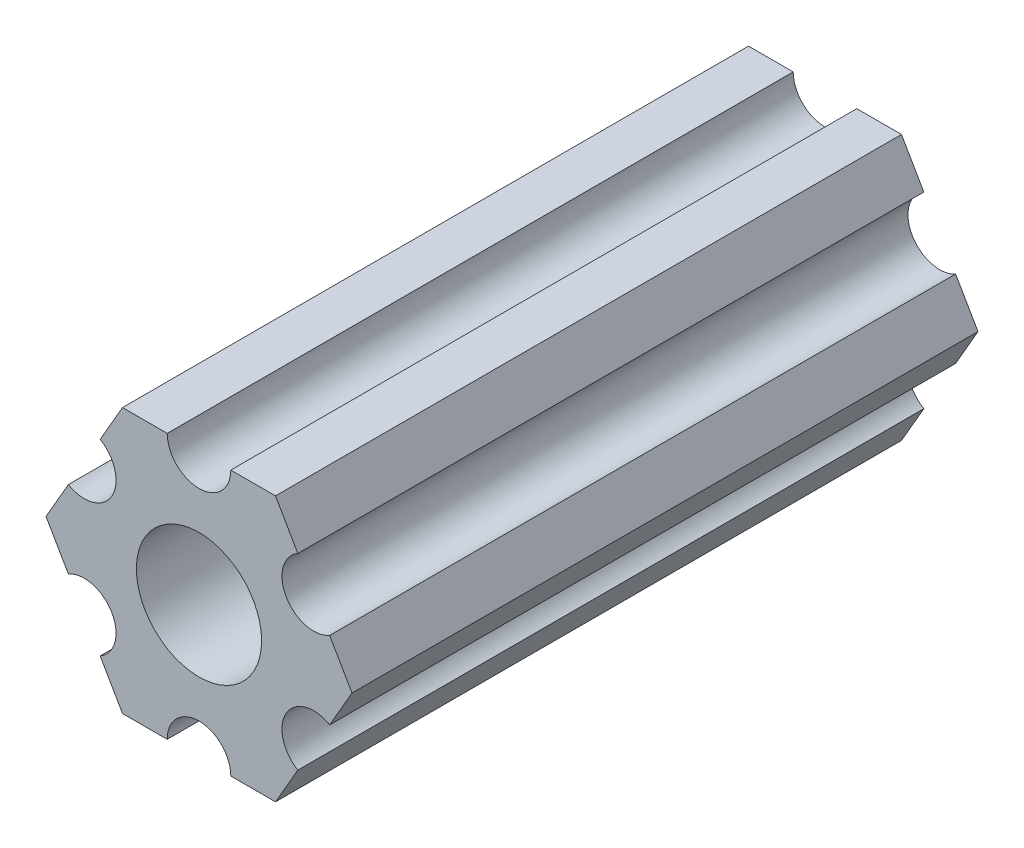
SolidWorks part; units mm, degrees
material "Churro - 6005A-T61"
ref_plane "Plano frontal" through (0, 0, 0) normal (0, 0, 1) x (1, 0, 0)
ref_plane "Plano superior" through (0, 0, 0) normal (0, 1, 0) x (1, 0, 0)
ref_plane "Plano direito" through (0, 0, 0) normal (1, 0, 0) x (0, 0, -1)
sketch "Esboço1" plane through (0, 0, 0) normal (0, 0, 1) x (1, 0, 0)
  line L1 (3.6662, 6.35) -> (-3.6662, 6.35)
  line L2 (-3.6662, 6.35) -> (-7.3323, 0)
  line L3 (-7.3323, 0) -> (-3.6662, -6.35)
  line L4 (-3.6662, -6.35) -> (3.6662, -6.35)
  line L5 (3.6662, -6.35) -> (7.3323, 0)
  line L6 (7.3323, 0) -> (3.6662, 6.35)
  circle A0 centre (0, 0) radius 6.35 construction
  circle A1 centre (0, 0) radius 3
  circle A2 centre (0, 6.35) radius 1.524
  circle A3 centre (5.4993, 3.175) radius 1.524
  circle A4 centre (5.4993, -3.175) radius 1.524
  circle A5 centre (0, -6.35) radius 1.524
  circle A6 centre (-5.4993, -3.175) radius 1.524
  circle A7 centre (-5.4993, 3.175) radius 1.524
  point P24 (0, 0)
  dimension "D1" = 12.7
  dimension "D2" = 6
  dimension "D3" = 3.048
  dimension "D4" = 6
extrude "Ressalto-extrusão1" add sketch "Esboço1" along normal blind 30 contours A7 L2 L3 A6 L4 A5 L5 A4 L6 A3 L1 A2 A1
